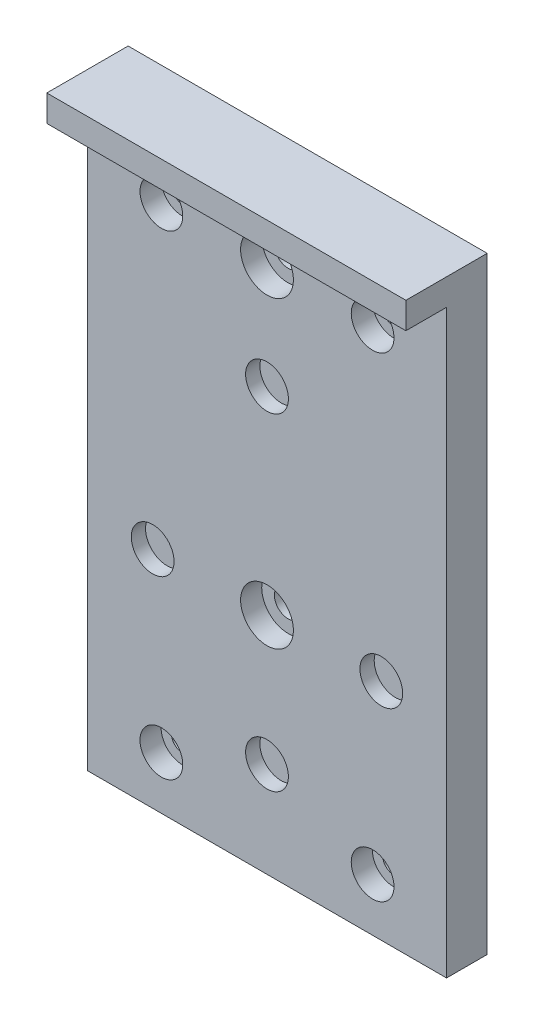
SolidWorks part; units mm, degrees
ref_plane "Front Plane" through (0, 0, 0) normal (0, 0, 1) x (1, 0, 0)
ref_plane "Top Plane" through (0, 0, 0) normal (0, 1, 0) x (1, 0, 0)
ref_plane "Right Plane" through (0, 0, 0) normal (1, 0, 0) x (0, 0, -1)
sketch "Sketch1" plane through (0, 0, 0) normal (0, 0, 1) x (1, 0, 0)
  line L0 (0, -45) -> (0, -41) construction
  line L1 (-34, 55) -> (34, 55)
  line L2 (-34, 55) -> (-34, -55)
  line L3 (-34, -55) -> (34, -55)
  line L4 (34, 55) -> (34, -55)
  line L5 (-34, 55) -> (34, -55) construction
  line L6 (-34, -55) -> (34, 55) construction
  line L7 (-20, 45) -> (20, 45) construction
  line L8 (-20, 45) -> (-20, -45) construction
  line L9 (-20, -45) -> (20, -45) construction
  line L10 (20, 45) -> (20, -45) construction
  line L11 (-20, 45) -> (20, -45) construction
  line L12 (-20, -45) -> (20, 45) construction
  line L13 (0, 25) -> (-21.6506, -12.5) construction
  line L14 (-21.6506, -12.5) -> (21.6506, -12.5) construction
  line L15 (21.6506, -12.5) -> (0, 25) construction
  circle A0 centre (20, 45) radius 2.1
  circle A1 centre (-20, 45) radius 2.1
  circle A2 centre (20, -45) radius 2.1
  circle A3 centre (-20, -45) radius 2.1
  circle A4 centre (0, 0) radius 25 construction
  circle A5 centre (21.6506, -12.5) radius 4.05
  circle A6 centre (0, 25) radius 4.05
  circle A7 centre (-21.6506, -12.5) radius 4.05
  circle A9 centre (0, -36.95) radius 4.05
  circle A10 centre (0, 45) radius 2.6
  circle A11 centre (0, -12.5) radius 2.6
  point P0 (0, 0)
  point P6 (0, 0)
extrude "Boss-Extrude1" add sketch "Sketch1" along normal blind 7.7
sketch "Sketch2" plane through (0, 0, 0) normal (0, 0, -1) x (-1, 0, 0)
  circle A0 centre (-21.6506, -12.5) radius 6.3046
  circle A1 centre (0, 25) radius 7.3343
  circle A2 centre (21.6506, -12.5) radius 8.114
  circle A3 centre (0, -36.95) radius 11.0737
extrude "Boss-Extrude2" add sketch "Sketch2" against normal blind 5
sketch "Sketch3" plane through (0, 0, 7.7) normal (0, 0, -1) x (-1, 0, 0)
  circle A0 centre (-20, 45) radius 4.05
  circle A1 centre (20, 45) radius 4.05
  circle A2 centre (-20, -45) radius 4.05
  circle A3 centre (20, -45) radius 4.05
  circle A4 centre (0, 45) radius 5
  circle A5 centre (0, -12.5) radius 5
extrude "Cut-Extrude1" cut sketch "Sketch3" along normal blind 4
sketch "Sketch4" plane through (0, 0, 7.7) normal (0, 0, 1) x (1, 0, 0)
  line L0 (-34, 55) -> (34, 55)
  line L1 (34, 55) -> (34, 60)
  line L2 (34, 60) -> (-34, 60)
  line L3 (-34, 60) -> (-34, 55)
extrude "Boss-Extrude3" add sketch "Sketch4" along normal blind 7.7 and the other way blind 7.7
